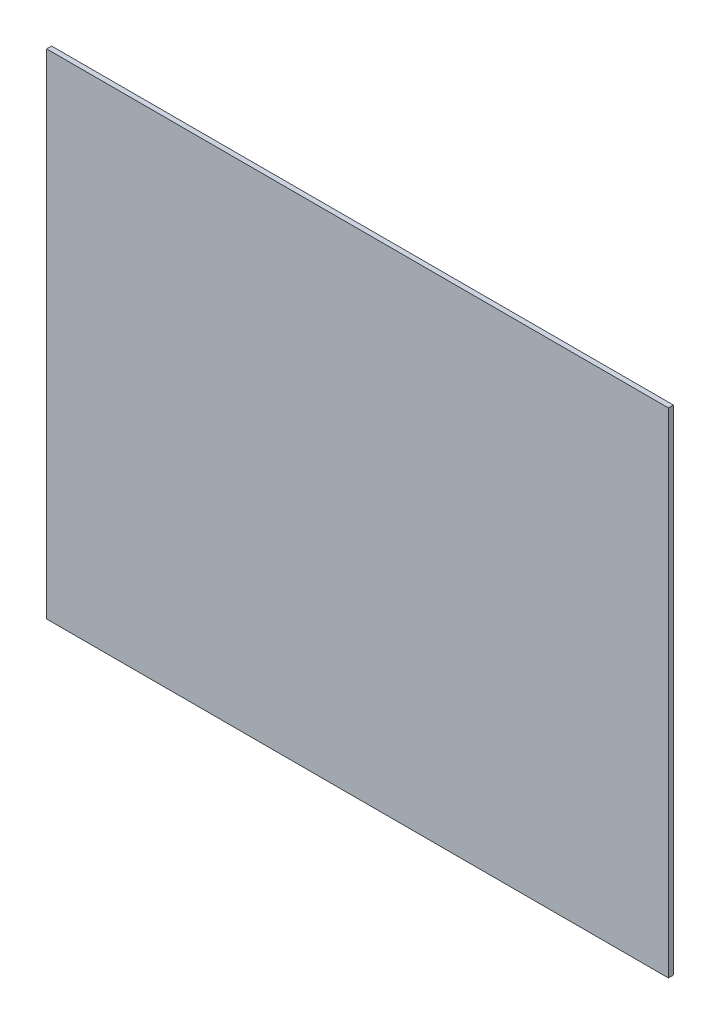
SolidWorks part; units mm, degrees
ref_plane "Alzado" through (0, 0, 0) normal (0, 0, 1) x (1, 0, 0)
ref_plane "Planta" through (0, 0, 0) normal (0, 1, 0) x (1, 0, 0)
ref_plane "Vista lateral" through (0, 0, 0) normal (1, 0, 0) x (0, 0, -1)
sketch "Croquis1" plane through (0, 0, 0) normal (0, 0, 1) x (1, 0, 0)
  line L1 (-125, 99.25) -> (125, 99.25)
  line L2 (-125, 99.25) -> (-125, -99.25)
  line L3 (-125, -99.25) -> (125, -99.25)
  line L4 (125, 99.25) -> (125, -99.25)
  line L5 (-125, 99.25) -> (125, -99.25) construction
  line L6 (-125, -99.25) -> (125, 99.25) construction
  point P0 (0, 0)
  dimension "D1" = 250
  dimension "D2" = 198.5
extrude "Saliente-Extruir1" add sketch "Croquis1" along normal blind 2
